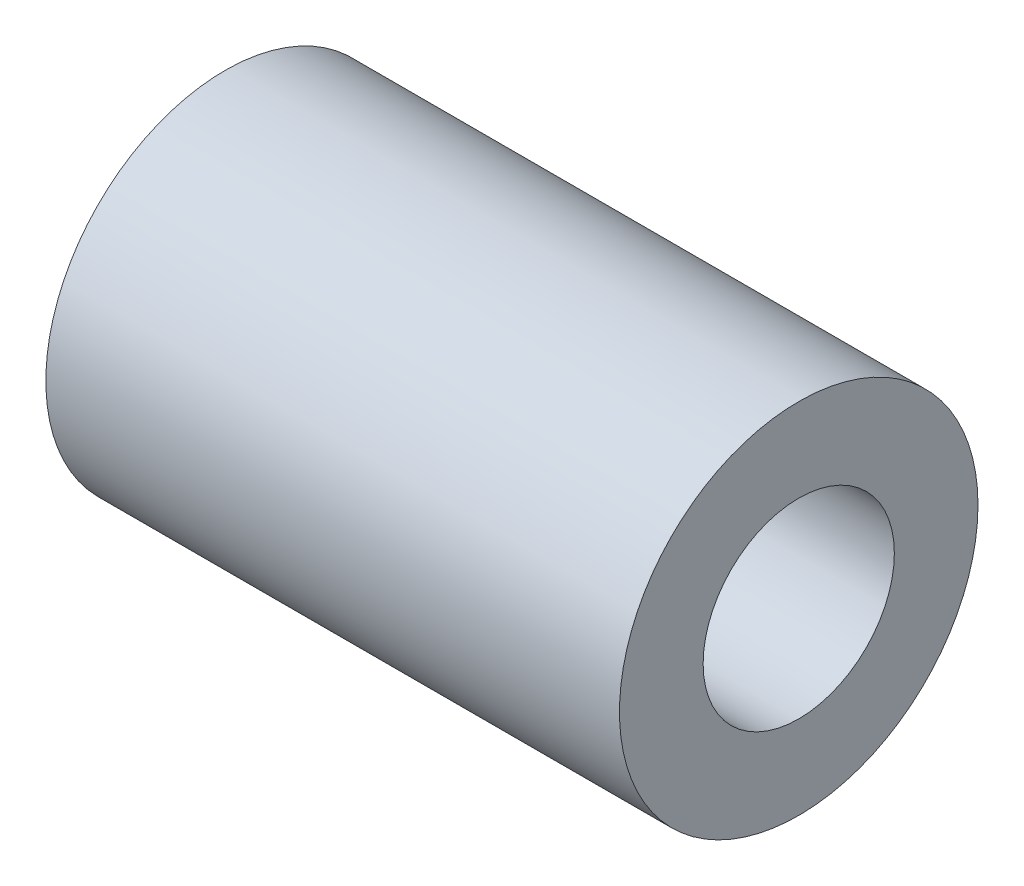
SolidWorks part; units mm, degrees
ref_plane "前视基准面" through (0, 0, 0) normal (0, 0, 1) x (1, 0, 0)
ref_plane "上视基准面" through (0, 0, 0) normal (0, 1, 0) x (1, 0, 0)
ref_plane "右视基准面" through (0, 0, 0) normal (1, 0, 0) x (0, 0, -1)
sketch "草图1" plane through (0, 0, 0) normal (1, 0, 0) x (0, 0, -1)
  circle A0 centre (0, 0) radius 4
  circle A1 centre (0, 0) radius 7.5
  dimension "D1" = 15
  dimension "D2" = 8
extrude "凸台-拉伸1" add sketch "草图1" along normal blind 24
